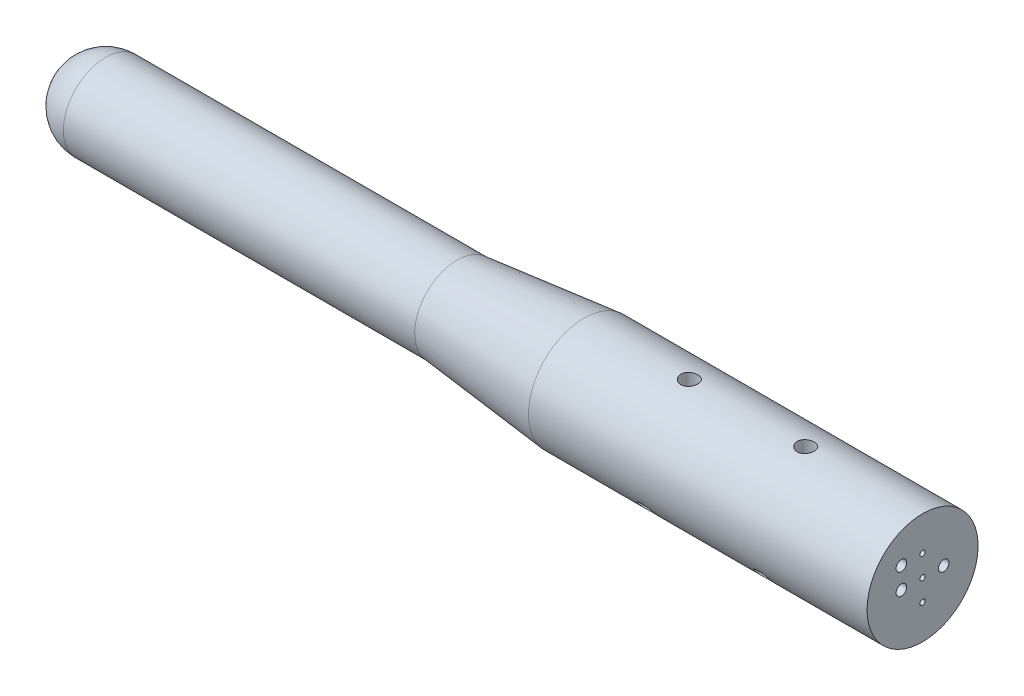
SolidWorks part; units mm, degrees
material "Tungsten"
ref_plane "Front Plane" through (0, 0, 0) normal (0, 0, 1) x (1, 0, 0)
ref_plane "Top Plane" through (0, 0, 0) normal (0, 1, 0) x (1, 0, 0)
ref_plane "Right Plane" through (0, 0, 0) normal (1, 0, 0) x (0, 0, -1)
sketch "Sketch1" plane through (0, 0, 0) normal (0, 0, 1) x (1, 0, 0)
  line L0 (0, 0) -> (257.81, 0) construction
  line L1 (12.7, 12.7) -> (118.11, 12.7)
  line L4 (118.11, 12.7) -> (156.21, 16.6623)
  line L5 (156.21, 16.6623) -> (257.81, 16.6623)
  line L6 (257.81, 16.6623) -> (257.81, 0)
  line L7 (118.11, 12.7) -> (156.21, 12.7) construction
  line L8 (156.21, 12.7) -> (156.21, 16.6623) construction
  line L9 (0, 0) -> (12.7, 0) construction
  line L10 (0, 0) -> (257.81, 0) construction
  line L11 (0, 0) -> (257.81, 0)
  arc A1 (12.7, 12.7) -> (0, 0) centre (12.7, 0) ccw
  dimension "D2" = 105.41
  dimension "D3" = 38.1
  dimension "D4" = 101.6
revolve "Revolve1" add sketch "Sketch1" angle 360 about L11
sketch "Sketch3" plane through (257.81, 0, 0) normal (1, 0, 0) x (0, 0, -1)
  line L0 (-6.35, 0) -> (6.35, 0) construction
  line L1 (0, -6.35) -> (0, 6.35) construction
  circle A0 centre (0, 0) radius 0.7937
  circle A1 centre (6.35, 0) radius 0.7938
  circle A2 centre (-6.35, 0) radius 0.7938
  circle A3 centre (0, 6.35) radius 0.7938
  circle A4 centre (0, -6.35) radius 0.7938
extrude "Cut-Extrude1" cut sketch "Sketch3" against normal through all
sketch "Sketch4" plane through (257.81, 0, 0) normal (1, 0, 0) x (0, 0, -1)
  circle A0 centre (-6.35, 0) radius 1.5875
  circle A1 centre (6.35, 0) radius 1.5875
extrude "Cut-Extrude2" cut sketch "Sketch4" against normal blind 12.7
ref_plane "Plane1" through (0, 16.6623, 0) normal (0, 1, 0) x (1, 0, 0)
sketch "Sketch5" plane through (0, 16.6623, 0) normal (0, 1, 0) x (1, 0, 0)
  line L0 (257.81, 0) -> (222.758, 0) construction
  line L1 (257.81, -16.6623) -> (257.81, 16.6623) construction
  line L2 (222.758, 0) -> (187.833, 0) construction
  point P1 (222.758, 0)
  point P5 (187.833, 0)
  point P12 (187.833, 0)
  point P15 (222.758, 0)
  dimension "D1" = 35.052
  dimension "D2" = 34.925
hole_wizard "Tap Drill for #10 Helicoil2" positions "Sketch5" profile "Sketch8" hole size "#10-32" standard "ANSI Inch"
sketch "Sketch8" plane through (222.758, 16.6623, 0) normal (1, 0, 0) x (0, 0, 1)
  line L0 (0, 0) -> (0, 8.3312)
  line L1 (0, 8.3312) -> (2.5527, 6.7974)
  line L2 (2.5527, 6.7974) -> (2.5527, 0)
  line L5 (2.5527, 0) -> (0, 0)
  line L10 (0, 8.3312) -> (-2.5527, 6.7974) construction
  line L11 (0, -6.35) -> (0, 107.95) construction
  dimension "Hole Dia." = 5.1054
  dimension "Hole Depth" = 8.3312
  dimension "Drill Angle" = 118
pattern_circular "CirPattern2" count 3 every 115 about axis through (257.81, 0, 0) along (-1, 0, 0) of "Tap Drill for #10 Helicoil2"
ref_plane "Plane2" through (0.0248, 0, 0) normal (1, 0, 0) x (0, 0, -1)
sketch "Sketch9" plane through (0.0248, 0, 0) normal (1, 0, 0) x (0, 0, -1)
  point P0 (0, 0)
sketch "Sketch11" plane through (257.81, 0, 0) normal (1, 0, 0) x (0, 0, -1)
  line L0 (0, 6.35) -> (-6.35, 6.35) construction
  line L1 (-6.35, 6.35) -> (-6.35, 0) construction
  circle A0 centre (-6.35, 6.35) radius 1.5875
  dimension "D1" = 3.175
extrude "Cut-Extrude3" cut sketch "Sketch11" against normal blind 12.7
